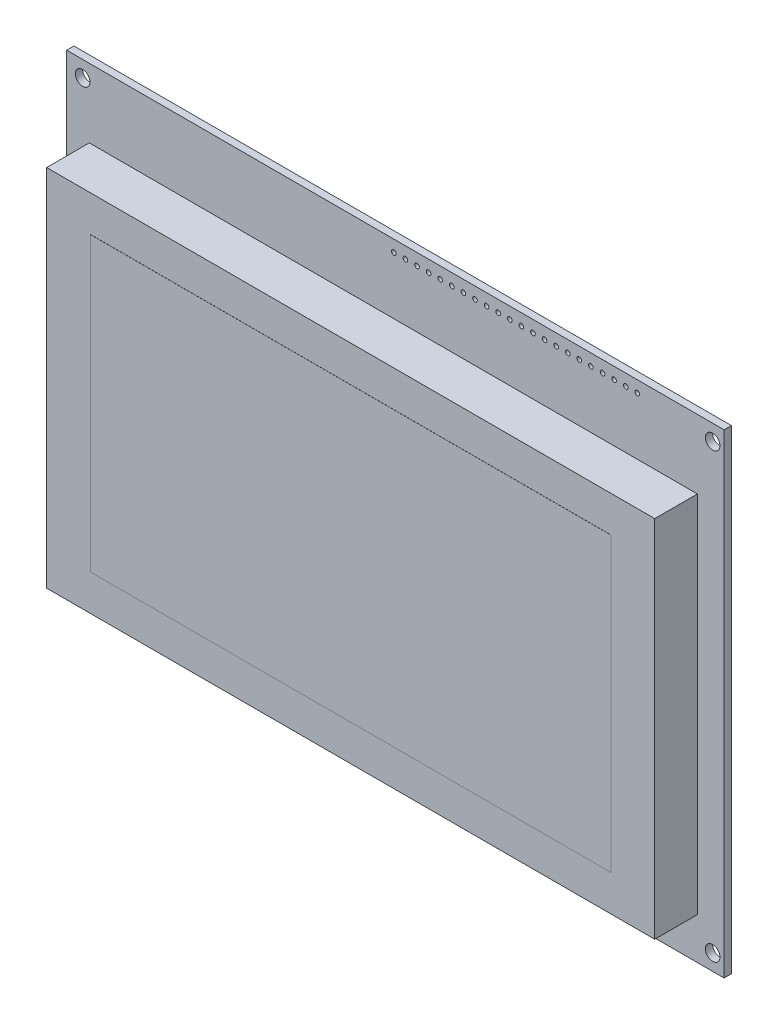
SolidWorks part; units mm, degrees
ref_plane "Front Plane" through (0, 0, 0) normal (0, 0, 1) x (1, 0, 0)
ref_plane "Top Plane" through (0, 0, 0) normal (0, 1, 0) x (1, 0, 0)
ref_plane "Right Plane" through (0, 0, 0) normal (1, 0, 0) x (0, 0, -1)
sketch "Sketch1" plane through (0, 0, 0) normal (0, 0, 1) x (1, 0, 0)
  line L0 (-68.5, 48.5) -> (69.5, 48.5) construction
  line L1 (-72, -52) -> (72, -52)
  line L2 (-72, -52) -> (-72, 52)
  line L3 (-72, 52) -> (72, 52)
  line L4 (72, -52) -> (72, 52)
  line L5 (0, 52) -> (0, -52) construction
  line L6 (-72, 0) -> (72, 0) construction
  line L7 (69.5, 48.5) -> (69.5, -48.5) construction
  line L8 (69.5, -48.5) -> (-68.5, -48.5) construction
  line L9 (-68.5, -48.5) -> (-68.5, 48.5) construction
  line L10 (72, 49.46) -> (-72, 49.46) construction
  line L11 (53, 49.46) -> (50.46, 49.46) construction
  circle A0 centre (-68.5, 48.5) radius 1.6
  circle A1 centre (69.5, 48.5) radius 1.6
  circle A2 centre (69.5, -48.5) radius 1.6
  circle A3 centre (-68.5, -48.5) radius 1.6
  circle A4 centre (53, 49.46) radius 0.508
  circle A26 centre (50.46, 49.46) radius 0.508
  circle A27 centre (47.92, 49.46) radius 0.508
  circle A28 centre (45.38, 49.46) radius 0.508
  circle A29 centre (42.84, 49.46) radius 0.508
  circle A30 centre (40.3, 49.46) radius 0.508
  circle A31 centre (37.76, 49.46) radius 0.508
  circle A32 centre (35.22, 49.46) radius 0.508
  circle A33 centre (32.68, 49.46) radius 0.508
  circle A34 centre (30.14, 49.46) radius 0.508
  circle A35 centre (27.6, 49.46) radius 0.508
  circle A36 centre (25.06, 49.46) radius 0.508
  circle A37 centre (22.52, 49.46) radius 0.508
  circle A38 centre (19.98, 49.46) radius 0.508
  circle A39 centre (17.44, 49.46) radius 0.508
  circle A40 centre (14.9, 49.46) radius 0.508
  circle A41 centre (12.36, 49.46) radius 0.508
  circle A42 centre (9.82, 49.46) radius 0.508
  circle A43 centre (7.28, 49.46) radius 0.508
  circle A44 centre (4.74, 49.46) radius 0.508
  circle A45 centre (2.2, 49.46) radius 0.508
  circle A46 centre (-0.34, 49.46) radius 0.508
  point P0 (0, 0)
  dimension "D3" = 3.2
  dimension "D8" = 1.016
  dimension "D12" = 2.54
  dimension "D1" = 104
  dimension "D2" = 144
  dimension "D4" = 138
  dimension "D5" = 97
  dimension "D6" = 3.5
  dimension "D7" = 3.5
  dimension "D10" = 19
  dimension "D11" = 2.54
  dimension "D9" = 22
extrude "Boss-Extrude1" add sketch "Sketch1" along normal blind 1.6
sketch "Sketch2" plane through (0, 0, 1.6) normal (0, 0, 1) x (1, 0, 0)
  line L0 (72, 52) -> (-72, 52) construction
  line L1 (-67.042, -42.9) -> (66.158, -42.9)
  line L2 (-67.042, -42.9) -> (-67.042, 36.9)
  line L3 (-67.042, 36.9) -> (66.158, 36.9)
  line L4 (66.158, -42.9) -> (66.158, 36.9)
  line L5 (-0.442, 36.9) -> (-0.442, -42.9) construction
  line L6 (-67.042, -3) -> (66.158, -3) construction
  line L7 (72, -52) -> (72, 52) construction
  point P0 (-0.442, -3)
  point P4 (0, 0)
  point P5 (-2.6207, -3.5679)
  dimension "D1" = 79.8
  dimension "D2" = 133.2
  dimension "D3" = 15.1
  dimension "D4" = 5.842
extrude "Boss-Extrude2" add sketch "Sketch2" along normal blind 9.3472
sketch "Sketch3" plane through (0, 0, 10.9472) normal (0, 0, 1) x (1, 0, 0)
  line L1 (-57.442, 29) -> (56.558, 29)
  line L2 (-57.442, 29) -> (-57.442, -35)
  line L3 (-57.442, -35) -> (56.558, -35)
  line L4 (56.558, 29) -> (56.558, -35)
  line L5 (-57.442, 29) -> (56.558, -35) construction
  line L6 (-57.442, -35) -> (56.558, 29) construction
  line L7 (53.533, -30.6298) -> (-54.417, -30.6298) construction
  line L8 (53.533, -30.6298) -> (53.533, 24.6298) construction
  line L9 (53.533, 24.6298) -> (-54.417, 24.6298) construction
  line L10 (66.158, -42.9) -> (66.158, 36.9)
  line L11 (66.158, 36.9) -> (-67.042, 36.9)
  line L12 (-67.042, 36.9) -> (-67.042, -42.9)
  line L13 (-67.042, -42.9) -> (66.158, -42.9)
  line L14 (66.158, -42.9) -> (66.158, 36.9) construction
  line L15 (66.158, 36.9) -> (-67.042, 36.9) construction
  line L16 (-67.042, 36.9) -> (-67.042, -42.9) construction
  line L17 (-67.042, -42.9) -> (66.158, -42.9) construction
  line L18 (-54.417, -30.6298) -> (-54.417, 24.6298) construction
  line L19 (-0.442, 24.6298) -> (-0.442, -30.6298) construction
  line L20 (53.533, -3) -> (-54.417, -3) construction
  point P4 (-0.442, -3)
  point P5 (-0.442, -3)
  point P12 (-67.042, -3)
  point P13 (-57.442, -3)
  point P14 (-0.442, 29)
  point P15 (-0.442, 36.9)
  dimension "D1" = 114
  dimension "D2" = 64
  dimension "D4" = 107.95
  dimension "D5" = 55.2597
  dimension "D3" = 0
extrude "Boss-Extrude3" add sketch "Sketch3" along normal blind 0.0254 separate body
